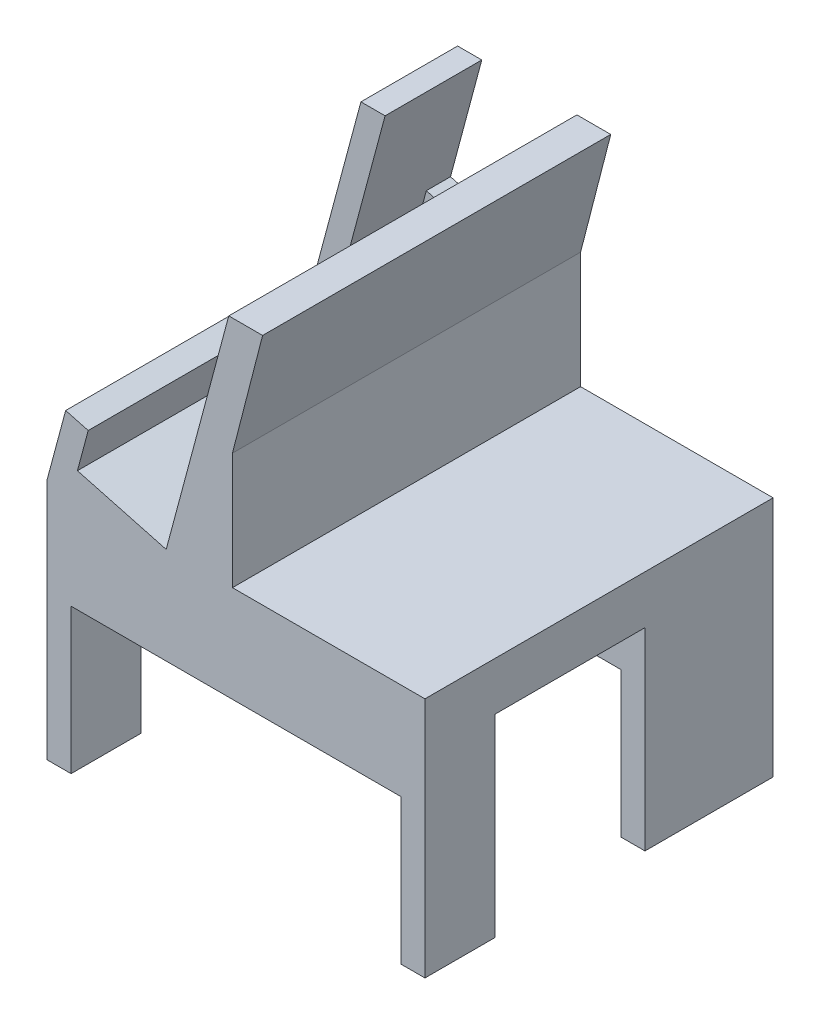
SolidWorks part; units mm, degrees
ref_plane "前基準面" through (0, 0, 0) normal (0, 0, 1) x (1, 0, 0)
ref_plane "上基準面" through (0, 0, 0) normal (0, 1, 0) x (1, 0, 0)
ref_plane "右基準面" through (0, 0, 0) normal (1, 0, 0) x (0, 0, -1)
sketch "草圖1" plane through (0, 0, 0) normal (0, 0, 1) x (1, 0, 0)
  line L1 (-56.4104, -6.4286) -> (-51.4104, -6.4286)
  line L2 (-56.4104, -6.4286) -> (-56.4104, -36.4286)
  line L3 (-56.4104, -36.4286) -> (-51.4104, -36.4286)
  line L4 (-51.4104, -6.4286) -> (-51.4104, -36.4286)
  line L5 (-56.4104, -6.4286) -> (21.7764, -6.4286)
  line L6 (-56.4104, -6.4286) -> (-56.4104, 13.5714)
  line L7 (-56.4104, 13.5714) -> (21.7764, 13.5714)
  line L8 (21.7764, -6.4286) -> (21.7764, 13.5714)
  line L9 (21.7764, -6.4286) -> (16.7764, -6.4286)
  line L10 (21.7764, -6.4286) -> (21.7764, -36.4286)
  line L11 (21.7764, -36.4286) -> (16.7764, -36.4286)
  line L12 (16.7764, -6.4286) -> (16.7764, -36.4286)
  dimension "D1" = 30
  dimension "D2" = 5
  dimension "D3" = 5
  dimension "D4" = 20
extrude "填料-伸長1" add sketch "草圖1" along normal blind 72 contours L5 L8 L7 L6 L1 | L5 L12 L11 L10
sketch "草圖2" plane through (0, -6.4286, 0) normal (0, -1, 0) x (1, 0, 0)
  line L0 (-51.4104, 72) -> (-51.4104, 0) construction
  line L1 (-51.4104, 26.5) -> (16.7764, 26.5)
  line L2 (-51.4104, 26.5) -> (-51.4104, 57.5)
  line L3 (-51.4104, 57.5) -> (16.7764, 57.5)
  line L4 (16.7764, 26.5) -> (16.7764, 57.5)
  line L5 (16.7764, 72) -> (16.7764, 0) construction
  line L6 (-51.4104, 72) -> (16.7764, 72) construction
  line L7 (-51.4104, 0) -> (16.7764, 0) construction
  dimension "D1" = 14.5
  dimension "D2" = 26.5
extrude "除料-伸長1" cut sketch "草圖2" against normal blind 10
sketch "草圖3" plane through (0, -36.4286, 0) normal (0, -1, 0) x (1, 0, 0)
  line L0 (-51.4104, 72) -> (-51.4104, 0) construction
  line L1 (-51.4104, 26.5) -> (-56.4104, 26.5)
  line L2 (-51.4104, 26.5) -> (-51.4104, 57.5)
  line L3 (-51.4104, 57.5) -> (-56.4104, 57.5)
  line L4 (-56.4104, 26.5) -> (-56.4104, 57.5)
  line L5 (-56.4104, 72) -> (-56.4104, 0) construction
  line L6 (-56.4104, 0) -> (-51.4104, 0) construction
  line L7 (-56.4104, 72) -> (-51.4104, 72) construction
  point P10 (-53.9104, 57.5)
  dimension "D1" = 26.5
  dimension "D2" = 14.5
extrude "除料-伸長3" cut sketch "草圖3" against normal blind 40
sketch "草圖4" plane through (0, -36.4286, 0) normal (0, -1, 0) x (1, 0, 0)
  line L0 (16.7764, 72) -> (16.7764, 0) construction
  line L1 (16.7764, 57.5) -> (21.7764, 57.5)
  line L2 (16.7764, 57.5) -> (16.7764, 26.5)
  line L3 (16.7764, 26.5) -> (21.7764, 26.5)
  line L4 (21.7764, 57.5) -> (21.7764, 26.5)
  line L5 (21.7764, 72) -> (21.7764, 0) construction
  line L6 (21.7764, 72) -> (16.7764, 72) construction
  line L7 (21.7764, 0) -> (16.7764, 0) construction
  dimension "D1" = 14.5
  dimension "D2" = 26.5
extrude "除料-伸長4" cut sketch "草圖4" against normal blind 40
sketch "草圖10" plane through (0, 0, 0) normal (0, 0, 1) x (1, 0, 0)
  line L0 (-56.4104, 13.5714) -> (-43.4694, 61.8677)
  line L1 (-56.4104, 13.5714) -> (21.7764, 13.5714) construction
  line L2 (-43.4694, 61.8677) -> (-38.4694, 61.8677)
  line L3 (-38.4694, 61.8677) -> (-44.9399, 37.7196)
  line L4 (-44.9399, 37.7196) -> (-26.5873, 32.802)
  line L6 (-26.5873, 32.802) -> (-18.7992, 61.8677)
  line L7 (-18.7992, 61.8677) -> (-11.7992, 61.8677)
  line L8 (-11.7992, 61.8677) -> (-18.039, 37.6589)
  line L9 (-18.039, 37.6589) -> (-18.039, 13.5714)
  line L10 (-18.039, 13.5714) -> (-56.4104, 13.5714)
  dimension "D1" = 50
  dimension "D2" = 75
  dimension "D3" = 5
  dimension "D4" = 19
  dimension "D5" = 25
  dimension "D6" = 30.091
  dimension "D7" = 7
  dimension "D8" = 7
  dimension "D9" = 25
extrude "填料-伸長6" add sketch "草圖10" along normal blind 5
sketch "草圖11" plane through (0, 0, 5) normal (0, 0, 1) x (1, 0, 0)
  line L0 (-56.4104, 13.5714) -> (-43.4694, 61.8677)
  line L1 (-43.4694, 61.8677) -> (-38.4694, 61.8677)
  line L2 (-38.4694, 61.8677) -> (-50.0927, 18.489)
  line L3 (-50.0927, 18.489) -> (-31.7401, 13.5714)
  line L4 (-56.4104, 13.5714) -> (-18.039, 13.5714) construction
  line L5 (-31.7401, 13.5714) -> (-18.7992, 61.8677)
  line L6 (-18.7992, 61.8677) -> (-11.7992, 61.8677)
  line L7 (-11.7992, 61.8677) -> (-18.039, 37.6589)
  line L8 (-18.039, 37.6589) -> (-18.039, 13.5714)
  line L9 (-18.039, 13.5714) -> (-31.7401, 13.5714)
  line L10 (-56.4104, 13.5714) -> (-31.7401, 13.5714)
  line M11 (-56.4104, 13.5714) -> (-18.039, 13.5714)
  line M12 (-18.039, 13.5714) -> (-18.039, 37.6589)
  line M13 (-18.039, 37.6589) -> (-11.7992, 61.8677)
  line M14 (-11.7992, 61.8677) -> (-18.7992, 61.8677)
  line M15 (-18.7992, 61.8677) -> (-26.5873, 32.802)
  line M17 (-44.9399, 37.7196) -> (-38.4694, 61.8677)
  line M18 (-38.4694, 61.8677) -> (-43.4694, 61.8677)
  line M19 (-43.4694, 61.8677) -> (-56.4104, 13.5714)
  dimension "D1" = 19
extrude "填料-伸長7" add sketch "草圖11" along normal up to surface (67 mm away) contours L3 L2 M17 M18 M19 M11 | L5 M11 M12 M13 M14 M15 up to face at (-17.317, -16.4286, 72)
sketch "草圖12" plane through (-56.0245, 15.0117, 0) normal (-0.9659, 0.2588, 0) x (0, 0, 1)
  line L1 (20, 50.2294) -> (72, 50.2294)
  line L2 (20, 50.2294) -> (20, 13.5089)
  line L3 (20, 13.5089) -> (72, 13.5089)
  line L4 (72, 50.2294) -> (72, 13.5089)
  line L5 (72, 48.5089) -> (72, -1.4911) construction
  line L6 (0, 48.5089) -> (0, -1.4911) construction
  line L7 (72, -1.4911) -> (0, -1.4911) construction
  dimension "D1" = 20
  dimension "D2" = 15
extrude "除料-伸長5" cut sketch "草圖12" against normal blind 5
equation "\"ㄓ\"=4.80833"
